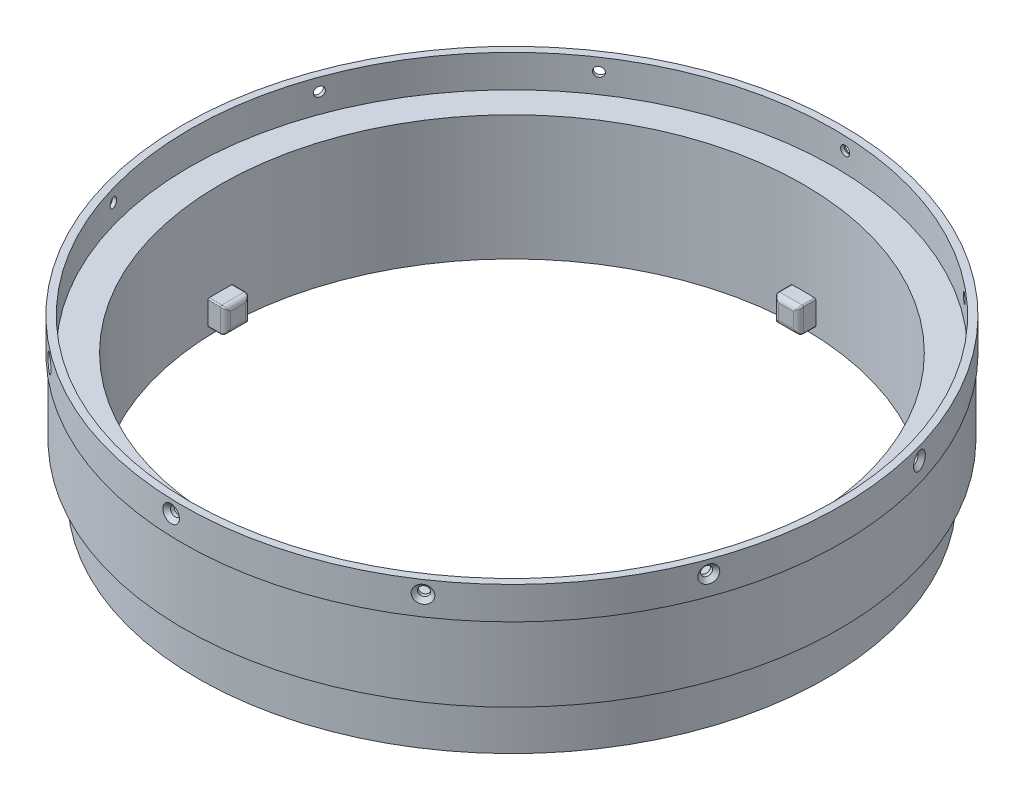
SolidWorks part; units mm, degrees
ref_plane "Front Plane" through (0, 0, 0) normal (0, 0, 1) x (1, 0, 0)
ref_plane "Top Plane" through (0, 0, 0) normal (0, 1, 0) x (1, 0, 0)
ref_plane "Right Plane" through (0, 0, 0) normal (1, 0, 0) x (0, 0, -1)
sketch "Sketch1" plane through (0, 0, 0) normal (0, 0, 1) x (1, 0, 0)
  line L0 (0, 49.1435) -> (0, -38.5417) construction
  line L1 (83.82, 42.3241) -> (83.82, 34.0691)
  line L2 (83.82, 34.0691) -> (83.439, 34.0691)
  line L3 (83.439, 34.0691) -> (83.439, 15.0191)
  line L4 (83.439, 15.0191) -> (79.9338, 15.0191)
  line L5 (79.9338, 15.0191) -> (79.9338, 2.3191)
  line L6 (79.9338, 2.3191) -> (74.168, 2.3191)
  line L7 (74.168, 2.3191) -> (74.168, 34.0691)
  line L8 (74.168, 34.0691) -> (81.9531, 34.0691)
  line L9 (81.9531, 34.0691) -> (81.9531, 42.3241)
  line L10 (81.9531, 42.3241) -> (83.82, 42.3241)
  dimension "D1" = 19.05
  dimension "D2" = 0.381
  dimension "D3" = 8.255
  dimension "D4" = 31.75
  dimension "D5" = 12.7
  dimension "D6" = 1.8669
  dimension "D7" = 5.7658
  dimension "D8" = 83.82
  dimension "D9" = 3.5052
revolve "Revolve1" add sketch "Sketch1" angle 360 about L0
hole_wizard "CSK for M2 Flat Head Machine Screw1" positions "3DSketch2" profile "Sketch2" countersink size "M2" standard "ANSI Metric" end condition through all
sketch3d "3DSketch2"
  point P0 (80.574, 39.0781, -23.1003)
sketch "Sketch2" plane through (80.574, 39.0781, -23.1003) normal (0, 1, 0) x (-0.2756, 0, -0.9613)
  line L0 (0, 0) -> (0, 201.4765)
  line L1 (0, 201.4765) -> (1.2, 201.4765)
  line L2 (1.2, 201.4765) -> (1.2, 1)
  line L3 (1.2, 1) -> (2.2, 0)
  line L5 (2.2, 0) -> (0, 0)
  line L6 (-1.2, 1) -> (-2.2, 0) construction
  line L11 (0, -6.35) -> (0, 107.95) construction
  dimension "Thru Hole Dia." = 2.4
  dimension "Thru Hole Depth" = 201.4765
  dimension "Near C'Sink Dia." = 4.4
  dimension "Near C'Sink Angle" = 90
pattern_circular "CirPattern1" count 10 over 360 about axis through (0, 49.1435, 0) along (0, 1, 0) of "CSK for M2 Flat Head Machine Screw1"
sketch3d "3DSketch4"
  point P0 (-2.4273, 4.97, 79.8969)
ref_plane "Plane3" through (0, 0, 74.422) normal (0, 0, 1) x (1, 0, 0)
sketch "Sketch14" plane through (0, 0, 74.422) normal (0, 0, 1) x (1, 0, 0)
  line L0 (-79.9338, 2.3191) -> (79.9338, 2.3191) construction
  line L1 (-3.175, 10.5741) -> (3.175, 10.5741)
  line L2 (-3.175, 10.5741) -> (-3.175, 4.2241)
  line L3 (-3.175, 4.2241) -> (3.175, 4.2241)
  line L4 (3.175, 10.5741) -> (3.175, 4.2241)
  line L5 (-3.175, 10.5741) -> (3.175, 4.2241) construction
  line L6 (-3.175, 4.2241) -> (3.175, 10.5741) construction
  point P0 (0, 7.3991)
  dimension "D1" = 6.35
  dimension "D2" = 5.08
extrude "Boss-Extrude1" add sketch "Sketch14" against normal blind 4.7625
fillet "Fillet1" radius 1.27 4 edges at (3.175, 7.3991, 69.6595) (0, 4.2241, 69.6595) (-3.175, 7.3991, 69.6595) (0, 10.5741, 69.6595)
fillet "Fillet2" radius 0.3175 8 edges at (-2.803, 4.5961, 70.0315) (2.803, 4.5961, 70.0315) (-2.803, 10.2022, 70.0315) (2.803, 10.2022, 70.0315) (-3.175, 4.2241, 72.5148) (3.175, 4.2241, 72.5148) (-3.175, 10.5741, 72.5148) (3.175, 10.5741, 72.5148)
pattern_circular "CirPattern2" count 4 over 360 about axis through (0, 49.1435, 0) along (0, 1, 0) of "Boss-Extrude1", "Fillet1", "Fillet2"
